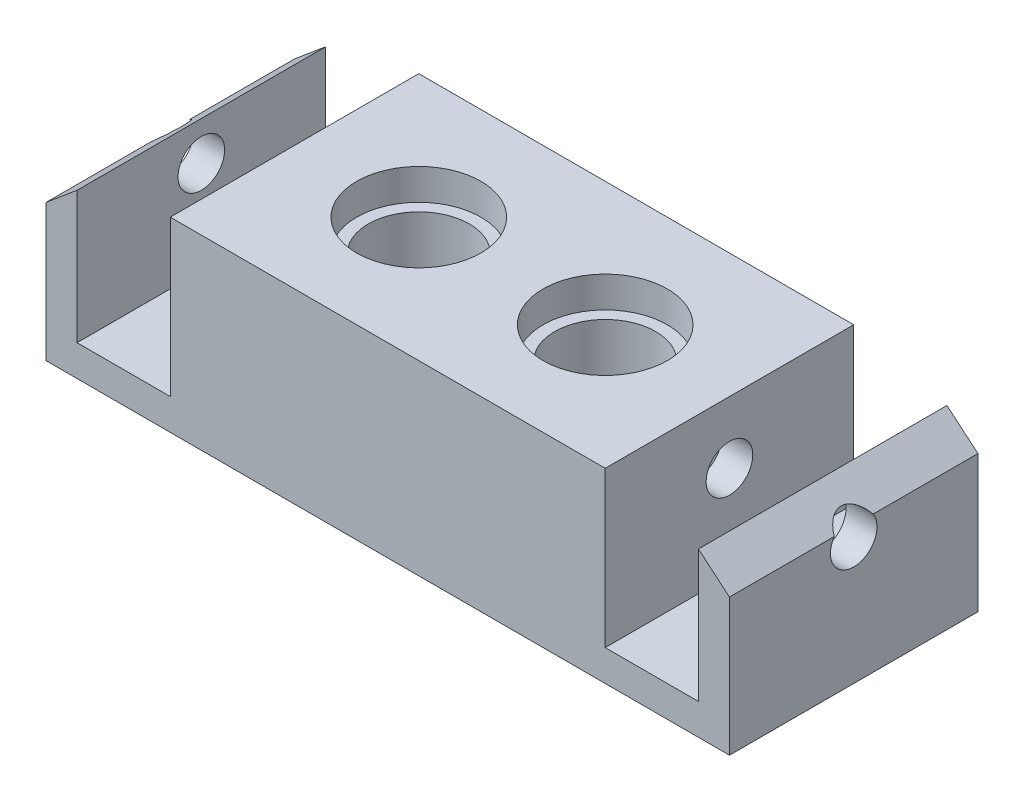
SolidWorks part; units mm, degrees
ref_plane "Front Plane" through (0, 0, 0) normal (0, 0, 1) x (1, 0, 0)
ref_plane "Top Plane" through (0, 0, 0) normal (0, 1, 0) x (1, 0, 0)
ref_plane "Right Plane" through (0, 0, 0) normal (1, 0, 0) x (0, 0, -1)
sketch "Sketch1" plane through (0, 0, 0) normal (0, 0, 1) x (1, 0, 0)
  line L1 (0, 0) -> (22, 0)
  line L2 (0, 0) -> (0, 6)
  line L3 (0, 6) -> (22, 6)
  line L4 (22, 0) -> (22, 6)
  dimension "D1" = 22
  dimension "D2" = 6
extrude "Boss-Extrude1" add sketch "Sketch1" against normal blind 8
sketch "Sketch2" plane through (0, 0, 0) normal (0, -1, 0) x (1, 0, 0)
  line L1 (0, -8) -> (0, 0) construction
  line L2 (5, -7) -> (17, -7)
  line L3 (5, -7) -> (5, -1)
  line L4 (5, -1) -> (17, -1)
  line L5 (17, -7) -> (17, -1)
  line L6 (5, -7) -> (17, -1) construction
  line L7 (5, -1) -> (17, -7) construction
  line L8 (0, -8) -> (22, -8) construction
  point P0 (11, -4)
  point P9 (0, -4)
  point P12 (11, -8)
  dimension "D1" = 6
  dimension "D2" = 12
extrude "Cut-Extrude1" cut sketch "Sketch2" against normal blind 5
sketch "Sketch3" plane through (0, 5, 0) normal (0, -1, 0) x (1, 0, 0)
  line L0 (17, -1) -> (5, -1) construction
  line L4 (5, -7) -> (17, -7) construction
  circle A0 centre (8, -4) radius 2.5
  circle A1 centre (14, -4) radius 2.5
  circle A2 centre (8, -4) radius 1.625
  circle A3 centre (14, -4) radius 1.625
  point P12 (11, -7)
  dimension "D2" = 5
  dimension "D4" = 3.25
  dimension "D1" = 6
  dimension "D3" = 3
  dimension "D5" = 3
extrude "Boss-Extrude4" add sketch "Sketch3" along normal blind 2 separate body
sketch "Sketch5" plane through (0, 6, 0) normal (0, 1, 0) x (1, 0, 0)
  circle A0 centre (8, 4) radius 2
  circle A1 centre (14, 4) radius 2
  circle A2 centre (14, 4) radius 2.5 construction
  circle A3 centre (8, 4) radius 2.5 construction
  dimension "D1" = 4
extrude "Cut-Extrude3" cut sketch "Sketch5" against normal blind 1
sketch "Sketch6" plane through (0, 0, 0) normal (0, 0, 1) x (1, 0, 0)
  line L5 (11, 6.1988) -> (11, -1.632) construction
  line L10 (0, 6) -> (0, 0) construction
  line L15 (22, 6) -> (0, 6) construction
  line L16 (1, 6) -> (4, 6)
  line L17 (1, 6) -> (1, 1)
  line L18 (1, 1) -> (4, 1)
  line L19 (4, 6) -> (4, 1)
  line L20 (18, 6) -> (18, 1)
  line L21 (21, 1) -> (18, 1)
  line L22 (21, 6) -> (21, 1)
  line L23 (21, 6) -> (18, 6)
  dimension "D1" = 5
  dimension "D2" = 3
  dimension "D3" = 1
  dimension "D4" = 11
extrude "Cut-Extrude4" cut sketch "Sketch6" against normal through all
sketch "Sketch8" plane through (22, 0, 0) normal (1, 0, 0) x (0, 0, -1)
  circle A0 centre (4, 4) radius 0.75
  dimension "D1" = 1.5
  dimension "D2" = 2
  dimension "D3" = 4
extrude "Cut-Extrude6" cut sketch "Sketch8" against normal blind 5.5
ref_plane "Plane1" through (11, 0, 0) normal (1, 0, 0) x (0, 0, -1)
mirror "Mirror1" about plane through (11, 0, 0) normal (1, 0, 0) of "Cut-Extrude6"
sketch "Sketch9" plane through (0, 0, 0) normal (0, 0, 1) x (1, 0, 0)
  line L4 (21, 6) -> (22, 6)
  line L5 (22, 0) -> (22, 6) construction
  line L6 (22, 6) -> (21, 6) construction
  line L7 (22, 6) -> (22, 4.4109)
  line L8 (22, 4.4109) -> (21, 5.25)
  line L9 (21, 1) -> (21, 6) construction
  line L10 (21, 5.25) -> (21, 6)
  dimension "D1" = 50
  dimension "D2" = 0.75
extrude "Cut-Extrude7" cut sketch "Sketch9" against normal blind 10
mirror "Mirror2" about plane through (11, 0, 0) normal (1, 0, 0) of "Cut-Extrude7"
